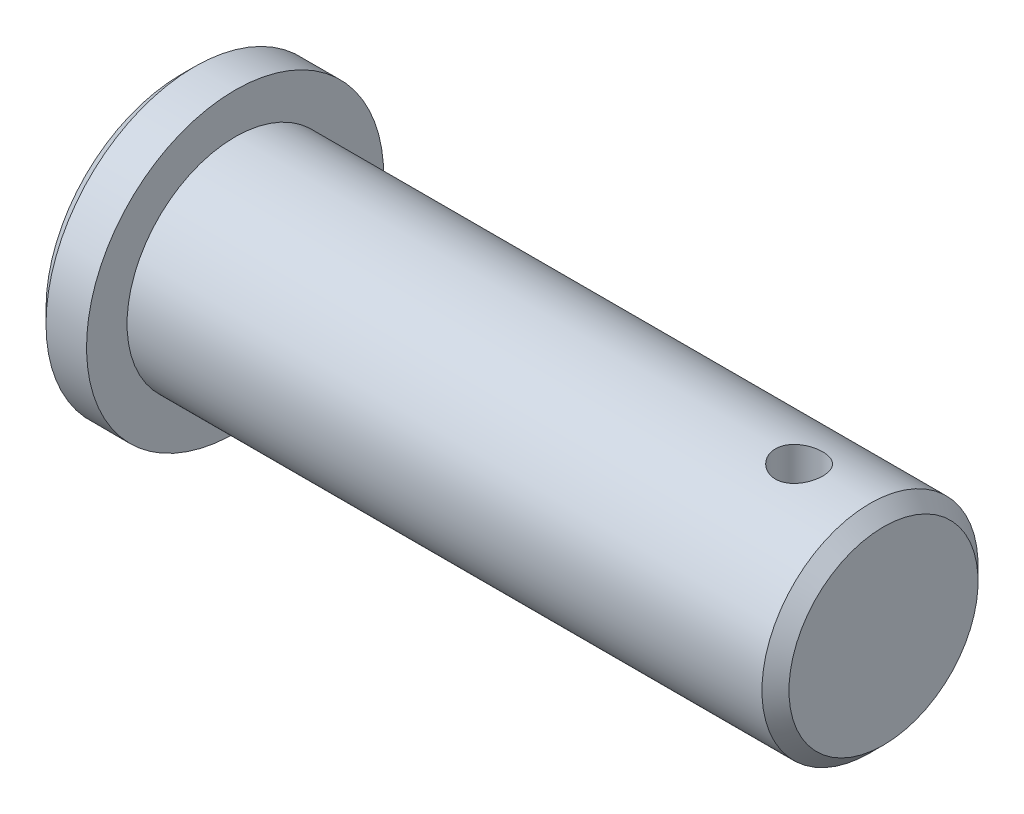
SolidWorks part; units mm, degrees
ref_plane "Płaszczyzna przednia" through (0, 0, 0) normal (0, 0, 1) x (1, 0, 0)
ref_plane "Płaszczyzna górna" through (0, 0, 0) normal (0, 1, 0) x (1, 0, 0)
ref_plane "Płaszczyzna prawa" through (0, 0, 0) normal (1, 0, 0) x (0, 0, -1)
sketch "Szkic1" plane through (0, 0, 0) normal (0, 0, 1) x (1, 0, 0)
  line L0 (0, 0) -> (0, 11)
  line L1 (0, 11) -> (4, 11)
  line L2 (4, 11) -> (4, 8)
  line L3 (4, 8) -> (52, 8)
  line L4 (52, 8) -> (52, 0)
  line L5 (52, 0) -> (0, 0)
  dimension "D1" = 4
  dimension "D2" = 11
  dimension "D3" = 8
  dimension "D4" = 48
revolve "Obrót1" add sketch "Szkic1" angle 360 about L5
sketch "Szkic2" plane through (0, 0, 0) normal (0, 1, 0) x (1, 0, 0)
  line L0 (0, 0) -> (45.75, 0) construction
  line L1 (0, 11) -> (0, -11) construction
  circle A0 centre (45.75, 0) radius 1.75
  dimension "D1" = 45.75
  dimension "D2" = 3.5
extrude "Wytnij-wyciągnięcie1" cut sketch "Szkic2" against normal through all and the other way through all
chamfer "Sfazowanie1" distance 1 angle 45 2 edges at (52, 8, 0) (0, 11, 0)
